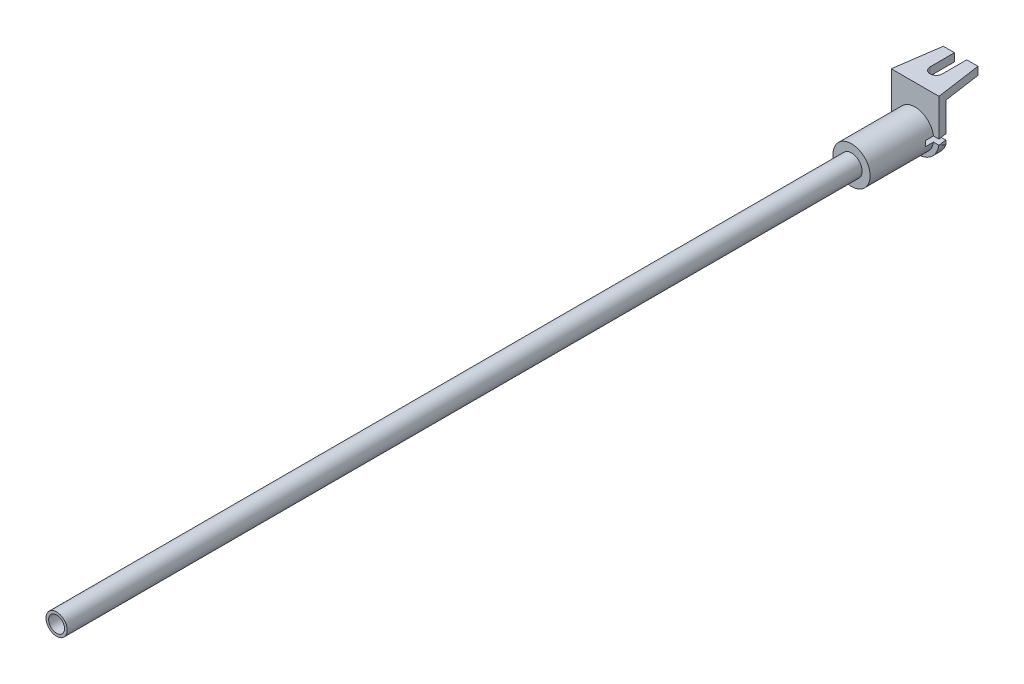
SolidWorks part; units mm, degrees
ref_plane "Plane1" through (0, 0, 0) normal (0, 0, 1) x (1, 0, 0)
ref_plane "Plane2" through (0, 0, 0) normal (0, 1, 0) x (1, 0, 0)
ref_plane "Plane3" through (0, 0, 0) normal (1, 0, 0) x (0, 0, -1)
sketch "Esquisse1" plane through (0, 0, 0) normal (0, 0, 1) x (1, 0, 0)
  circle A0 centre (0, 0) radius 3.5
  circle A1 centre (0, 0) radius 1
  dimension "D1" = 7
  dimension "D2" = 2
extrude "Base-Extrusion" add sketch "Esquisse1" along normal blind 12
sketch "Esquisse2" plane through (0, 0, 12) normal (0, 0, 1) x (1, 0, 0)
  circle A0 centre (0, 0) radius 2
  circle A1 centre (0, 0) radius 1.5
  dimension "D1" = 4
  dimension "D2" = 3
extrude "Boss.-Extru.1" add sketch "Esquisse2" along normal blind 150
sketch "Esquisse3" plane through (0, 0, 0) normal (1, 0, 0) x (0, 0, -1)
  line L0 (0, 0) -> (0, 7.5)
  line L1 (0, 7.5) -> (11.5, 7.5)
  line L2 (11.5, 7.5) -> (11.5, 6)
  line L3 (11.5, 6) -> (1.5, 6)
  line L4 (1.5, 6) -> (1.5, -4)
  line L5 (1.5, -4) -> (0, -4)
  line L6 (0, -4) -> (0, 0)
  dimension "D1" = 4
  dimension "D2" = 10
  dimension "D3" = 1.5
  dimension "D4" = 1.5
extrude "Boss.-Extru.2" add sketch "Esquisse3" along normal mid plane 9
fillet "Congé1" radius 4
sketch "Esquisse4" plane through (0, 0, -1.5) normal (0, 0, -1) x (-1, 0, 0)
  line L0 (0, 0) -> (-8, 0) construction
  line L1 (0, -0.5) -> (-7, -0.5)
  line L2 (0, 0.5) -> (-7, 0.5)
  line L3 (0, 0.5) -> (0, -0.5)
  line L4 (-7, 0.5) -> (-7, -0.5)
  dimension "D1" = 1
extrude "Enlèv. mat.-Extru.1" cut sketch "Esquisse4" against normal blind 3
sketch "Esquisse5" plane through (0, 7.5, 0) normal (0, 1, 0) x (-1, 0, 0)
  line L0 (0, -13.8721) -> (0, 2.7208) construction
  line L1 (0, 1.5) -> (0, 0) construction
  line L2 (1.1558, -8.5947) -> (1.1558, -3.9882)
  line L4 (-1.1558, -8.5947) -> (-1.1558, -3.9882)
  line L7 (-3.2725, -8.5947) -> (-4.5, 0)
  line L8 (3.2725, -8.5947) -> (4.5, 0)
  line L9 (-4.5, 0) -> (-6, 0)
  line L10 (4.5, 0) -> (6, 0)
  line L11 (-6, 0) -> (-6, -13)
  line L12 (6, 0) -> (6, -13)
  line L13 (-6, -13) -> (6, -13)
  line L14 (-3.2725, -8.5947) -> (-1.1558, -8.5947)
  line L17 (1.1558, -8.5947) -> (3.2725, -8.5947)
  arc A0 (1.1558, -3.9882) -> (-1.1558, -3.9882) centre (0, -3.9882) ccw
  point P21 (0, -13)
extrude "Enlèv. mat.-Extru.2" cut sketch "Esquisse5" against normal through all
